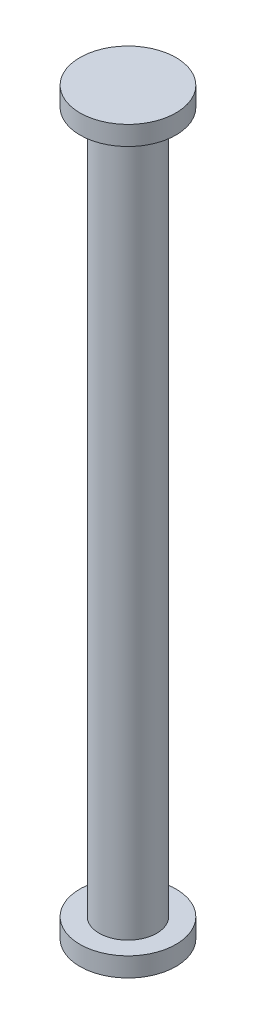
SolidWorks part; units mm, degrees
ref_plane "Front Plane" through (0, 0, 0) normal (0, 0, 1) x (1, 0, 0)
ref_plane "Top Plane" through (0, 0, 0) normal (0, 1, 0) x (1, 0, 0)
ref_plane "Right Plane" through (0, 0, 0) normal (1, 0, 0) x (0, 0, -1)
sketch "Sketch1" plane through (0, 0, 0) normal (0, 1, 0) x (1, 0, 0)
  circle A0 centre (0, 0) radius 2.5
extrude "Boss-Extrude1" add sketch "Sketch1" along normal blind 1
sketch "Sketch2" plane through (0, 1, 0) normal (0, 1, 0) x (1, 0, 0)
  circle A0 centre (0, 0) radius 1.5
extrude "Boss-Extrude2" add sketch "Sketch2" along normal blind 36.5
sketch "Sketch3" plane through (0, 37.5, 0) normal (0, 1, 0) x (1, 0, 0)
  circle A0 centre (0, 0) radius 2.5
extrude "Boss-Extrude3" add sketch "Sketch3" along normal blind 1
scale "Scale1" scale about centroid uniform scaling yes scale factor 1.8
